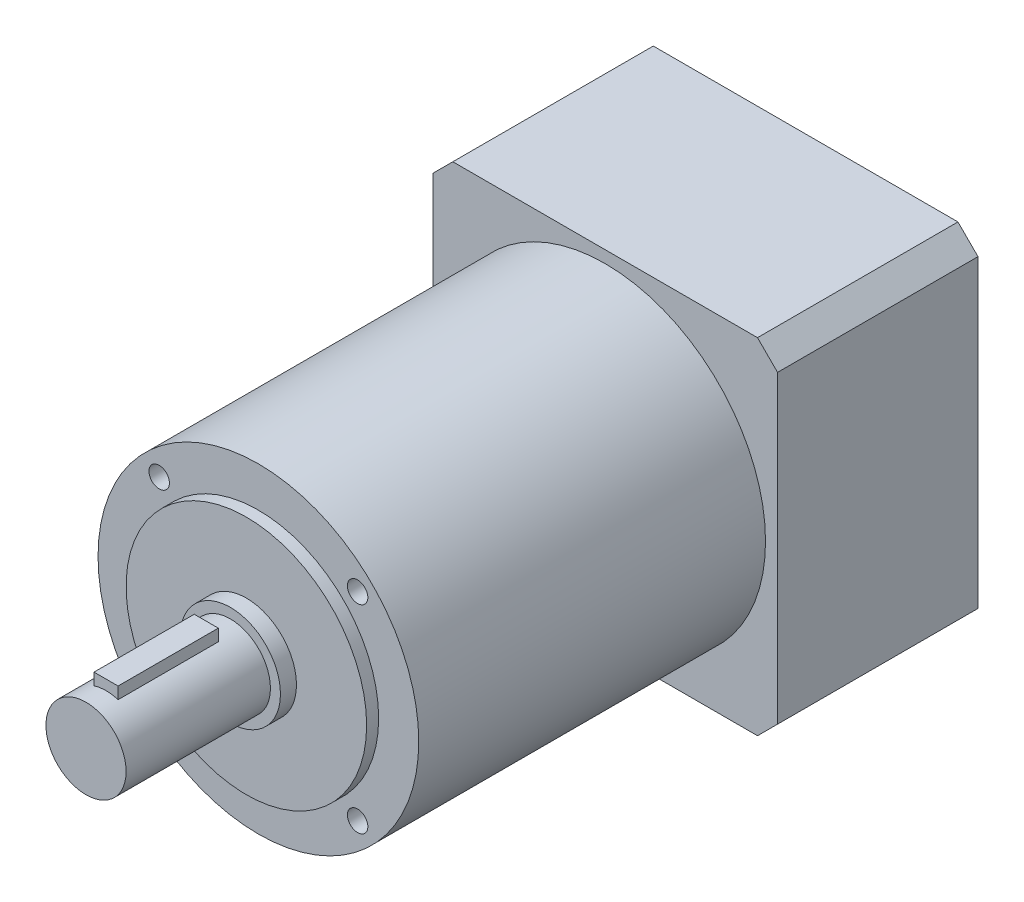
SolidWorks part; units mm, degrees
ref_plane "前视基准面" through (0, 0, 0) normal (0, 0, 1) x (1, 0, 0)
ref_plane "上视基准面" through (0, 0, 0) normal (0, 1, 0) x (1, 0, 0)
ref_plane "右视基准面" through (0, 0, 0) normal (1, 0, 0) x (0, 0, -1)
sketch "草图1" plane through (0, 0, 0) normal (0, 0, 1) x (1, 0, 0)
  line L1 (43, -43) -> (-43, -43)
  line L2 (43, -43) -> (43, 43)
  line L3 (43, 43) -> (-43, 43)
  line L4 (-43, -43) -> (-43, 43)
  line L5 (43, -43) -> (-43, 43) construction
  line L6 (43, 43) -> (-43, -43) construction
  point P0 (0, 0)
  dimension "D1" = 86
extrude "凸台-拉伸1" add sketch "草图1" along normal blind 50
sketch "草图2" plane through (0, 0, 50) normal (0, 0, 1) x (1, 0, 0)
  circle A0 centre (0, 0) radius 40
  dimension "D1" = 80
extrude "凸台-拉伸2" add sketch "草图2" along normal blind 86.5
sketch "草图3" plane through (0, 0, 136.5) normal (0, 0, 1) x (1, 0, 0)
  circle A0 centre (0, 0) radius 30
  dimension "D1" = 60
extrude "凸台-拉伸3" add sketch "草图3" along normal blind 3
sketch "草图4" plane through (0, 0, 139.5) normal (0, 0, 1) x (1, 0, 0)
  circle A0 centre (0, 0) radius 12.5
  dimension "D1" = 25
extrude "凸台-拉伸4" add sketch "草图4" along normal blind 4
sketch "草图5" plane through (0, 0, 143.5) normal (0, 0, 1) x (1, 0, 0)
  circle A0 centre (0, 0) radius 10
  dimension "D1" = 20
extrude "凸台-拉伸5" add sketch "草图5" along normal blind 36
sketch "草图7" plane through (0, 0, 0) normal (0, 1, 0) x (1, 0, 0)
  line L0 (0, -179.5) -> (0, -162) construction
  line L1 (3, -174.5) -> (-3, -174.5)
  line L2 (3, -174.5) -> (3, -149.5)
  line L3 (3, -149.5) -> (-3, -149.5)
  line L4 (-3, -174.5) -> (-3, -149.5)
  line L5 (3, -174.5) -> (-3, -149.5) construction
  line L6 (3, -149.5) -> (-3, -174.5) construction
  line L7 (-10, -179.5) -> (10, -179.5) construction
  point P0 (0, -162)
  dimension "D1" = 25
  dimension "D2" = 6
  dimension "D3" = 5
extrude "凸台-拉伸6" add sketch "草图7" along normal blind 12.5
sketch "草图8" plane through (0, 0, 0) normal (0, 0, -1) x (-1, 0, 0)
  circle A0 centre (0, 0) radius 36.5
extrude "切除-拉伸1" cut sketch "草图8" against normal blind 5
sketch "草图9" plane through (0, 0, 5) normal (0, 0, -1) x (-1, 0, 0)
  circle A0 centre (0, 0) radius 6.35
  dimension "D1" = 12.7
extrude "切除-拉伸2" cut sketch "草图9" against normal blind 30
sketch "草图10" plane through (0, 0, 0) normal (0, 0, -1) x (-1, 0, 0)
  line L1 (35, -35) -> (-35, -35) construction
  line L2 (35, -35) -> (35, 35) construction
  line L3 (35, 35) -> (-35, 35) construction
  line L4 (-35, -35) -> (-35, 35) construction
  line L5 (35, -35) -> (-35, 35) construction
  line L6 (35, 35) -> (-35, -35) construction
  circle A0 centre (0, 0) radius 49.4975 construction
  circle A1 centre (-35, 35) radius 2.1
  circle A2 centre (35, 35) radius 2.1
  circle A3 centre (35, -35) radius 2.1
  circle A4 centre (-35, -35) radius 2.1
  dimension "D1" = 70
  dimension "D2" = 4.2
extrude "切除-拉伸3" cut sketch "草图10" against normal blind 15
chamfer "倒角1" distance 5 angle 45 4 edges at (43, -43, 25) (-43, -43, 25) (43, 43, 25) (-43, 43, 25)
sketch "草图11" plane through (0, 0, 136.5) normal (0, 0, 1) x (1, 0, 0)
  line L1 (24.7487, 24.7487) -> (-24.7487, 24.7487) construction
  line L2 (24.7487, 24.7487) -> (24.7487, -24.7487) construction
  line L3 (24.7487, -24.7487) -> (-24.7487, -24.7487) construction
  line L4 (-24.7487, 24.7487) -> (-24.7487, -24.7487) construction
  line L5 (24.7487, 24.7487) -> (-24.7487, -24.7487) construction
  line L6 (24.7487, -24.7487) -> (-24.7487, 24.7487) construction
  circle A0 centre (0, 0) radius 35 construction
  circle A1 centre (-24.7487, 24.7487) radius 2.55
  circle A2 centre (24.7487, 24.7487) radius 2.55
  circle A3 centre (24.7487, -24.7487) radius 2.55
  circle A4 centre (-24.7487, -24.7487) radius 2.55
  point P0 (0, 0)
  dimension "D1" = 70
  dimension "D2" = 5.1
extrude "切除-拉伸4" cut sketch "草图11" against normal blind 15
